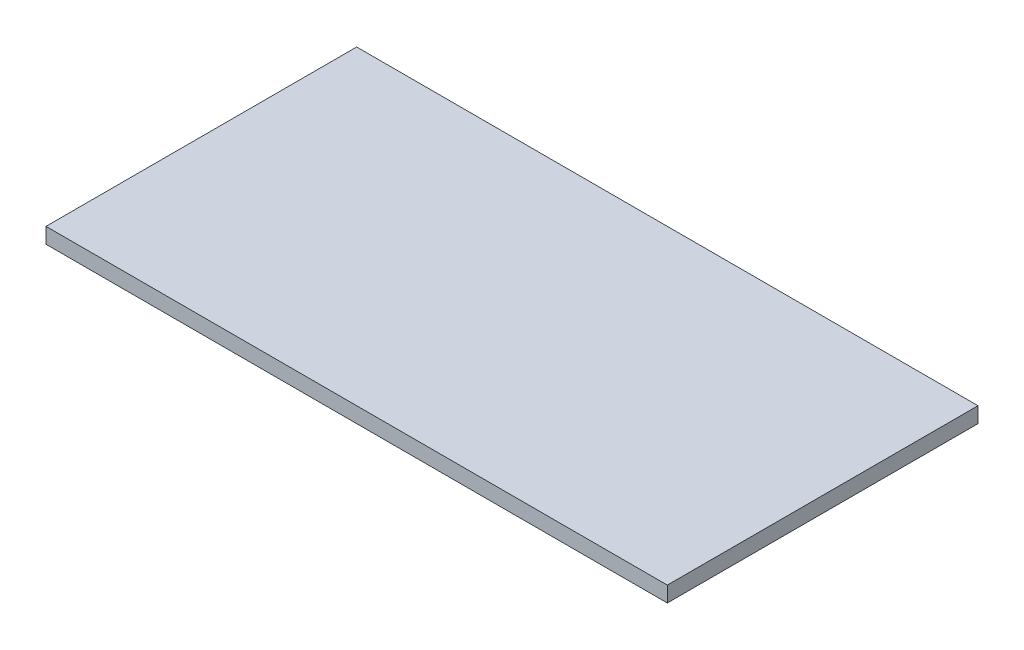
SolidWorks part; units mm, degrees
ref_plane "Front Plane" through (0, 0, 0) normal (0, 0, 1) x (1, 0, 0)
ref_plane "Top Plane" through (0, 0, 0) normal (0, 1, 0) x (1, 0, 0)
ref_plane "Right Plane" through (0, 0, 0) normal (1, 0, 0) x (0, 0, -1)
sketch "Sketch1" plane through (0, 0, 0) normal (0, 1, 0) x (1, 0, 0)
  line L1 (0, 0) -> (203.2, 0)
  line L2 (0, 0) -> (0, 101.6)
  line L3 (0, 101.6) -> (203.2, 101.6)
  line L4 (203.2, 0) -> (203.2, 101.6)
  dimension "D1" = 101.6
  dimension "D2" = 203.2
extrude "Boss-Extrude1" add sketch "Sketch1" along normal blind 5.08
equation "\"Foamcore\"= 0.2in"
equation "\"MDF\"= 0.2in"
equation "\"D1@Boss-Extrude1\"=\"Foamcore\""
